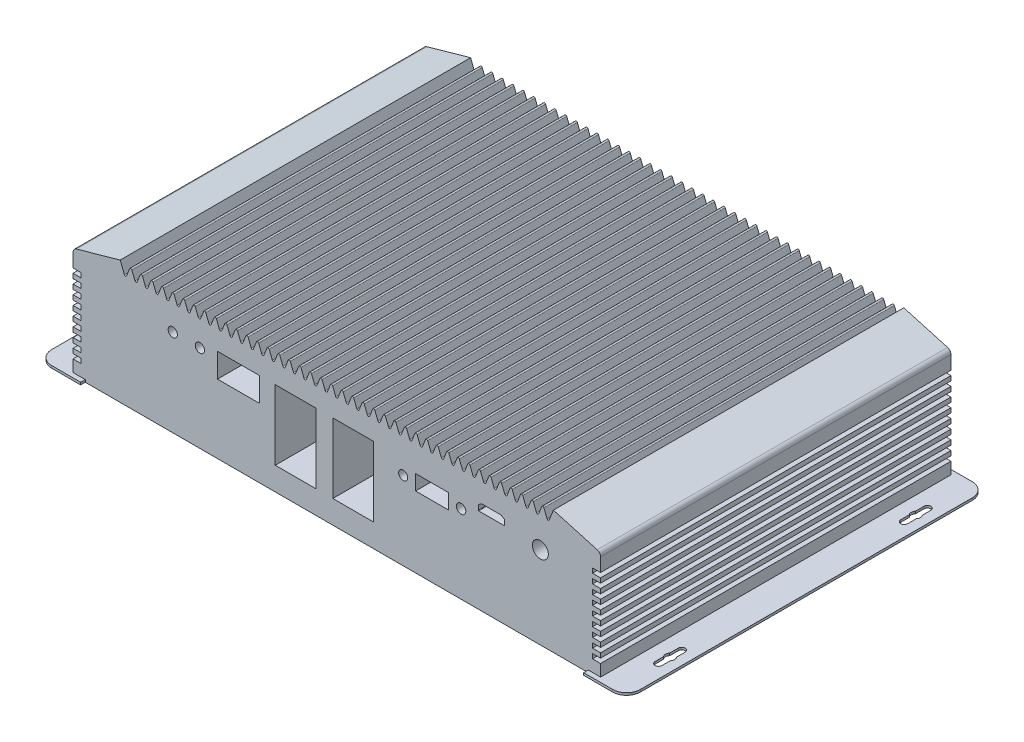
SolidWorks part; units mm, degrees
ref_plane "前视基准面" through (0, 0, 0) normal (0, 0, 1) x (1, 0, 0)
ref_plane "上视基准面" through (0, 0, 0) normal (0, 1, 0) x (1, 0, 0)
ref_plane "右视基准面" through (0, 0, 0) normal (1, 0, 0) x (0, 0, -1)
other "Configuration Table"
sketch "草图1" plane through (0, 0, 0) normal (0, 0, 1) x (1, 0, 0)
  line L0 (0, 0) -> (0, -13.9095) construction
  line L1 (-127.01, 0.5) -> (127.01, 0.5)
  line L2 (-127.01, 0.5) -> (-127.01, -0.5)
  line L3 (-127.01, -0.5) -> (127.01, -0.5)
  line L4 (127.01, 0.5) -> (127.01, -0.5)
  line L5 (-127.01, 0.5) -> (127.01, -0.5) construction
  line L6 (-127.01, -0.5) -> (127.01, 0.5) construction
  line L7 (108.53, 0.5) -> (108.53, 42.3)
  line L8 (108.53, 0.5) -> (-108.53, 0.5)
  line L9 (0, 0.5) -> (0, 46.5)
  line L10 (104.33, 46.5) -> (-104.33, 46.5)
  line L11 (-108.53, 0.5) -> (-108.53, 42.3)
  arc A0 (-104.33, 46.5) -> (-108.53, 42.3) centre (-104.33, 42.3) ccw
  arc A1 (104.33, 46.5) -> (108.53, 42.3) centre (104.33, 42.3) cw
  point P0 (0, 0)
  point P14 (-108.53, 46.5)
  point P19 (108.53, 46.5)
  dimension "D5" = 4.2
  dimension "D1" = 254.02
  dimension "D2" = 1
  dimension "D3" = 108.53
  dimension "D4" = 46
extrude "凸台-拉伸1" add sketch "草图1" against normal blind 155.2 contours L10 A0 L11 L1 L9 | A1 L10 L9 L8 L7 | L4 L1 L8 L2 L3
sketch "草图2" plane through (0, 0, 0) normal (0, 0, 1) x (1, 0, 0)
  line L0 (104.33, 46.5) -> (-104.33, 46.5) construction
  line L1 (104.33, 46.5) -> (-104.33, 46.5)
  line L2 (-108.53, 0.5) -> (-108.53, 42.3) construction
  line L3 (-108.53, 0.5) -> (-108.53, 42.3)
  line L4 (108.53, 0.5) -> (108.53, 42.3) construction
  line L5 (108.53, 0.5) -> (108.53, 42.3)
  line L6 (-127.01, -0.5) -> (127.01, -0.5) construction
  line L8 (-108.53, 0.5) -> (-108.53, -0.5)
  line L9 (-108.53, -0.5) -> (108.53, -0.5)
  line L10 (108.53, 0.5) -> (108.53, -0.5)
  arc A0 (108.53, 42.3) -> (104.33, 46.5) centre (104.33, 42.3) ccw construction
  arc A1 (-104.33, 46.5) -> (-108.53, 42.3) centre (-104.33, 42.3) ccw construction
  arc A2 (108.53, 42.3) -> (104.33, 46.5) centre (104.33, 42.3) ccw
  arc A3 (-104.33, 46.5) -> (-108.53, 42.3) centre (-104.33, 42.3) ccw
extrude "切除-拉伸1" cut sketch "草图2" against normal blind 2
ref_plane "基准面1" through (0, 0, -77.6) normal (0, 0, 1) x (1, 0, 0)
mirror "镜向1" about plane through (0, 0, -77.6) normal (0, 0, 1) of "切除-拉伸1"
sketch "草图3" plane through (0, -0.5, 0) normal (0, -1, 0) x (1, 0, 0)
  line L0 (-127.01, -77.6) -> (126.9569, -77.6) construction
  line L3 (0, -2) -> (0, -161.6283) construction
  line L5 (-121.245, -19.6) -> (-121.245, -29.6) construction
  line L6 (-119.745, -19.6) -> (-119.745, -29.6)
  line L7 (-122.745, -19.6) -> (-122.745, -29.6)
  line L8 (-104.33, -2) -> (104.33, -2)
  line L9 (-104.33, -2) -> (104.33, -2)
  line L10 (104.33, -2) -> (108.53, -2)
  line L11 (104.33, -2) -> (108.53, -2)
  line L12 (108.53, -2) -> (108.53, 0)
  line L13 (108.53, -2) -> (108.53, 0)
  line L14 (108.53, 0) -> (127.01, 0)
  line L15 (108.53, 0) -> (121.01, 0)
  line L16 (127.01, 0) -> (127.01, -155.2)
  line L17 (127.01, -6) -> (127.01, -149.2)
  line L18 (127.01, -155.2) -> (108.53, -155.2)
  line L19 (121.01, -155.2) -> (108.53, -155.2)
  line L20 (108.53, -155.2) -> (108.53, -153.2)
  line L21 (108.53, -155.2) -> (108.53, -153.2)
  line L22 (108.53, -153.2) -> (104.33, -153.2)
  line L23 (108.53, -153.2) -> (104.33, -153.2)
  line L24 (104.33, -153.2) -> (-104.33, -153.2)
  line L25 (104.33, -153.2) -> (-104.33, -153.2)
  line L26 (-104.33, -153.2) -> (-108.53, -153.2)
  line L27 (-104.33, -153.2) -> (-108.53, -153.2)
  line L28 (-108.53, -153.2) -> (-108.53, -155.2)
  line L29 (-108.53, -153.2) -> (-108.53, -155.2)
  line L30 (-108.53, -155.2) -> (-127.01, -155.2)
  line L31 (-108.53, -155.2) -> (-121.01, -155.2)
  line L32 (-127.01, -155.2) -> (-127.01, 0)
  line L33 (-127.01, -149.2) -> (-127.01, -6)
  line L34 (-127.01, 0) -> (-108.53, 0)
  line L35 (-121.01, 0) -> (-108.53, 0)
  line L36 (-108.53, 0) -> (-108.53, -2)
  line L37 (-108.53, 0) -> (-108.53, -2)
  line L38 (-108.53, -2) -> (-104.33, -2)
  line L39 (-108.53, -2) -> (-104.33, -2)
  line L40 (-121.245, -135.6) -> (-121.245, -125.6) construction
  line L41 (-127.01, 0) -> (-121.01, 0)
  line L42 (-127.01, 0) -> (-127.01, -6)
  line L43 (-127.01, -6) -> (-121.01, -6)
  line L44 (-121.01, 0) -> (-121.01, -6)
  line L45 (-127.01, -155.2) -> (-121.01, -155.2)
  line L46 (-127.01, -155.2) -> (-127.01, -149.2)
  line L47 (-127.01, -149.2) -> (-121.01, -149.2)
  line L48 (-121.01, -155.2) -> (-121.01, -149.2)
  line L49 (127.01, -155.2) -> (121.01, -155.2)
  line L50 (127.01, -155.2) -> (127.01, -149.2)
  line L51 (127.01, -149.2) -> (121.01, -149.2)
  line L52 (121.01, -155.2) -> (121.01, -149.2)
  line L53 (127.01, 0) -> (121.01, 0)
  line L54 (127.01, 0) -> (127.01, -6)
  line L55 (127.01, -6) -> (121.01, -6)
  line L56 (121.01, 0) -> (121.01, -6)
  line L57 (-119.745, -135.6) -> (-119.745, -125.6)
  line L58 (-122.745, -135.6) -> (-122.745, -125.6)
  line L59 (121.245, -135.6) -> (121.245, -125.6) construction
  line L60 (119.745, -135.6) -> (119.745, -125.6)
  line L61 (122.745, -135.6) -> (122.745, -125.6)
  line L62 (121.245, -19.6) -> (121.245, -29.6) construction
  line L63 (119.745, -19.6) -> (119.745, -29.6)
  line L64 (122.745, -19.6) -> (122.745, -29.6)
  circle A0 centre (-121.245, -24.6) radius 2
  arc A1 (-119.745, -19.6) -> (-122.745, -19.6) centre (-121.245, -19.6) ccw
  arc A2 (-122.745, -29.6) -> (-119.745, -29.6) centre (-121.245, -29.6) ccw
  arc A3 (-127.01, -6) -> (-121.01, 0) centre (-121.01, -6) cw
  arc A4 (121.01, 0) -> (127.01, -6) centre (121.01, -6) cw
  arc A5 (127.01, -149.2) -> (121.01, -155.2) centre (121.01, -149.2) cw
  arc A6 (-121.01, -155.2) -> (-127.01, -149.2) centre (-121.01, -149.2) cw
  circle A7 centre (-121.245, -130.6) radius 2
  arc A8 (-119.745, -135.6) -> (-122.745, -135.6) centre (-121.245, -135.6) cw
  arc A9 (-122.745, -125.6) -> (-119.745, -125.6) centre (-121.245, -125.6) cw
  circle A10 centre (121.245, -130.6) radius 2
  circle A11 centre (121.245, -24.6) radius 2
  arc A12 (119.745, -135.6) -> (122.745, -135.6) centre (121.245, -135.6) ccw
  arc A13 (122.745, -125.6) -> (119.745, -125.6) centre (121.245, -125.6) ccw
  arc A14 (119.745, -19.6) -> (122.745, -19.6) centre (121.245, -19.6) cw
  arc A15 (122.745, -29.6) -> (119.745, -29.6) centre (121.245, -29.6) cw
  point P9 (-121.245, -24.6)
  point P54 (-121.245, -130.6)
  point P65 (121.245, -130.6)
  point P72 (121.245, -24.6)
  line M4 (-127.01, -155.2) -> (-108.53, -155.2)
  line M8 (108.53, -155.2) -> (127.01, -155.2)
  line M9 (127.01, -155.2) -> (127.01, 0)
  line M10 (127.01, 0) -> (108.53, 0)
  line M14 (-108.53, 0) -> (-127.01, 0)
  line M15 (-127.01, 0) -> (-127.01, -155.2)
  dimension "D1" = 4
  dimension "D2" = 53
  dimension "D3" = 121.245
  dimension "D4" = 6
  dimension "D5" = 6
extrude "切除-拉伸2" cut sketch "草图3" against normal blind 2 contours A3 M15 M14 | A6 M4 M15 | A4 M10 M9 | L6 A1 L7 A0 | L6 A0 L7 | L7 A0 | L6 A0 | L7 A2 L6 A0 | A9 L58 A7 L57 | A7 L58 L57 | A7 L58 | A8 L57 A7 L58 | A14 L63 A11 L64 | A15 L64 A11 L63 | A5 M9 M8 | L61 A13 L60 A12 | A10
sketch "草图5" plane through (0, 0, -2) normal (0, 0, 1) x (1, 0, 0)
  line L0 (-108.53, -0.5) -> (108.53, -0.5) construction
  line L1 (0, -0.5) -> (-113.815, -0.5)
  line L2 (0, -0.5) -> (0, 52.72)
  line L4 (-113.815, -0.5) -> (-113.815, 5.5781)
  line L5 (-113.815, 11.5781) -> (-110.315, 11.5781)
  line L6 (-113.815, 7.5781) -> (-110.315, 7.5781)
  line L8 (-113.815, 5.5781) -> (-110.315, 5.5781)
  line L9 (-110.315, 7.5781) -> (-110.315, 5.5781)
  line L10 (-110.315, 11.5781) -> (-110.315, 9.5781)
  line L11 (-113.815, 9.5781) -> (-110.315, 9.5781)
  line L12 (-113.815, 15.5781) -> (-110.315, 15.5781)
  line L13 (-110.315, 15.5781) -> (-110.315, 13.5781)
  line L14 (-113.815, 13.5781) -> (-110.315, 13.5781)
  line L15 (-113.815, 19.5781) -> (-110.315, 19.5781)
  line L16 (-110.315, 19.5781) -> (-110.315, 17.5781)
  line L17 (-113.815, 17.5781) -> (-110.315, 17.5781)
  line L18 (-113.815, 23.5781) -> (-110.315, 23.5781)
  line L19 (-110.315, 23.5781) -> (-110.315, 21.5781)
  line L20 (-113.815, 21.5781) -> (-110.315, 21.5781)
  line L21 (-113.815, 27.5781) -> (-110.315, 27.5781)
  line L22 (-110.315, 27.5781) -> (-110.315, 25.5781)
  line L23 (-113.815, 25.5781) -> (-110.315, 25.5781)
  line L24 (-113.815, 31.5781) -> (-110.315, 31.5781)
  line L25 (-110.315, 31.5781) -> (-110.315, 29.5781)
  line L26 (-113.815, 29.5781) -> (-110.315, 29.5781)
  line L27 (-113.815, 35.5781) -> (-110.315, 35.5781)
  line L28 (-110.315, 35.5781) -> (-110.315, 33.5781)
  line L29 (-113.815, 33.5781) -> (-110.315, 33.5781)
  line L30 (-113.815, 39.5781) -> (-110.315, 39.5781)
  line L31 (-110.315, 39.5781) -> (-110.315, 37.5781)
  line L32 (-113.815, 37.5781) -> (-110.315, 37.5781)
  line L33 (-113.815, 39.5781) -> (-113.815, 45.4567)
  line L34 (-113.815, 35.5781) -> (-113.815, 37.5781)
  line L35 (-113.815, 31.5781) -> (-113.815, 33.5781)
  line L36 (-113.815, 27.5781) -> (-113.815, 29.5781)
  line L37 (-113.815, 23.5781) -> (-113.815, 25.5781)
  line L38 (-113.815, 19.5781) -> (-113.815, 21.5781)
  line L39 (-113.815, 15.5781) -> (-113.815, 17.5781)
  line L40 (-113.815, 11.5781) -> (-113.815, 13.5781)
  line L41 (-113.815, 7.5781) -> (-113.815, 9.5781)
  line L42 (0, 46.97) -> (-1.7969, 51.5463)
  line L43 (-2.7265, 51.5494) -> (-4.0913, 48.1406)
  line L44 (-5.0209, 48.1437) -> (-6.3569, 51.5463)
  line L45 (-7.2865, 51.5494) -> (-8.6513, 48.1406)
  line L46 (-9.5809, 48.1437) -> (-10.9169, 51.5463)
  line L47 (-4.56, 46.97) -> (-6.3569, 51.5463)
  line L48 (-11.8465, 51.5494) -> (-13.2113, 48.1406)
  line L49 (-14.1409, 48.1437) -> (-15.4769, 51.5463)
  line L50 (-9.5809, 48.1437) -> (-10.9169, 51.5463)
  line L51 (-16.4065, 51.5494) -> (-17.7713, 48.1406)
  line L52 (-18.7009, 48.1437) -> (-20.0369, 51.5463)
  line L53 (-14.1409, 48.1437) -> (-15.4769, 51.5463)
  line L54 (-20.9665, 51.5494) -> (-22.3313, 48.1406)
  line L55 (-23.2609, 48.1437) -> (-24.5969, 51.5463)
  line L56 (-18.7009, 48.1437) -> (-20.0369, 51.5463)
  line L57 (-25.5265, 51.5494) -> (-26.8913, 48.1406)
  line L58 (-27.8209, 48.1437) -> (-29.1569, 51.5463)
  line L59 (-23.2609, 48.1437) -> (-24.5969, 51.5463)
  line L60 (-30.0865, 51.5494) -> (-31.4513, 48.1406)
  line L61 (-32.3809, 48.1437) -> (-33.7169, 51.5463)
  line L62 (-27.8209, 48.1437) -> (-29.1569, 51.5463)
  line L63 (-34.6465, 51.5494) -> (-36.0113, 48.1406)
  line L64 (-36.9409, 48.1437) -> (-38.2769, 51.5463)
  line L65 (-32.3809, 48.1437) -> (-33.7169, 51.5463)
  line L66 (-39.2065, 51.5494) -> (-40.5713, 48.1406)
  line L67 (-41.5009, 48.1437) -> (-42.8369, 51.5463)
  line L68 (-36.9409, 48.1437) -> (-38.2769, 51.5463)
  line L69 (-43.7665, 51.5494) -> (-45.1313, 48.1406)
  line L70 (-46.0609, 48.1437) -> (-47.3969, 51.5463)
  line L71 (-41.5009, 48.1437) -> (-42.8369, 51.5463)
  line L72 (-48.3265, 51.5494) -> (-49.6913, 48.1406)
  line L73 (-50.6209, 48.1437) -> (-51.9569, 51.5463)
  line L74 (-46.0609, 48.1437) -> (-47.3969, 51.5463)
  line L75 (-52.8865, 51.5494) -> (-54.2513, 48.1406)
  line L76 (-55.1809, 48.1437) -> (-56.5169, 51.5463)
  line L77 (-50.6209, 48.1437) -> (-51.9569, 51.5463)
  line L78 (-57.4465, 51.5494) -> (-58.8113, 48.1406)
  line L79 (-59.7409, 48.1437) -> (-61.0769, 51.5463)
  line L80 (-55.1809, 48.1437) -> (-56.5169, 51.5463)
  line L81 (-62.0065, 51.5494) -> (-63.3713, 48.1406)
  line L82 (-64.3009, 48.1437) -> (-65.6369, 51.5463)
  line L83 (-59.7409, 48.1437) -> (-61.0769, 51.5463)
  line L84 (-66.5665, 51.5494) -> (-67.9313, 48.1406)
  line L85 (-68.8609, 48.1437) -> (-70.1969, 51.5463)
  line L86 (-64.3009, 48.1437) -> (-65.6369, 51.5463)
  line L87 (-71.1265, 51.5494) -> (-72.4913, 48.1406)
  line L88 (-73.4209, 48.1437) -> (-74.7569, 51.5463)
  line L89 (-68.8609, 48.1437) -> (-70.1969, 51.5463)
  line L90 (-75.6865, 51.5494) -> (-77.0513, 48.1406)
  line L91 (-77.9809, 48.1437) -> (-79.3169, 51.5463)
  line L92 (-73.4209, 48.1437) -> (-74.7569, 51.5463)
  line L93 (-80.2465, 51.5494) -> (-81.6113, 48.1406)
  line L94 (-82.5409, 48.1437) -> (-83.8769, 51.5463)
  line L95 (-77.9809, 48.1437) -> (-79.3169, 51.5463)
  line L96 (-84.8065, 51.5494) -> (-86.1713, 48.1406)
  line L97 (-87.1009, 48.1437) -> (-88.4369, 51.5463)
  line L98 (-82.5409, 48.1437) -> (-83.8769, 51.5463)
  line L99 (-89.3665, 51.5494) -> (-90.7313, 48.1406)
  line L100 (-91.6609, 48.1437) -> (-93.4578, 52.72)
  line L101 (-87.1009, 48.1437) -> (-88.4369, 51.5463)
  line L102 (-93.4578, 52.72) -> (-112.3586, 47.3814)
  arc A0 (-1.7969, 51.5463) -> (-2.7265, 51.5494) centre (-2.2623, 51.3635) ccw
  arc A1 (-4.0913, 48.1406) -> (-5.0209, 48.1437) centre (-4.5555, 48.3265) cw
  arc A2 (-6.3569, 51.5463) -> (-7.2865, 51.5494) centre (-6.8223, 51.3635) ccw
  arc A3 (-8.6513, 48.1406) -> (-9.5809, 48.1437) centre (-9.1155, 48.3265) cw
  arc A4 (-10.9169, 51.5463) -> (-11.8465, 51.5494) centre (-11.3823, 51.3635) ccw
  arc A5 (-13.2113, 48.1406) -> (-14.1409, 48.1437) centre (-13.6755, 48.3265) cw
  arc A6 (-15.4769, 51.5463) -> (-16.4065, 51.5494) centre (-15.9423, 51.3635) ccw
  arc A7 (-17.7713, 48.1406) -> (-18.7009, 48.1437) centre (-18.2355, 48.3265) cw
  arc A8 (-20.0369, 51.5463) -> (-20.9665, 51.5494) centre (-20.5023, 51.3635) ccw
  arc A9 (-22.3313, 48.1406) -> (-23.2609, 48.1437) centre (-22.7955, 48.3265) cw
  arc A10 (-24.5969, 51.5463) -> (-25.5265, 51.5494) centre (-25.0623, 51.3635) ccw
  arc A11 (-26.8913, 48.1406) -> (-27.8209, 48.1437) centre (-27.3555, 48.3265) cw
  arc A12 (-29.1569, 51.5463) -> (-30.0865, 51.5494) centre (-29.6223, 51.3635) ccw
  arc A13 (-31.4513, 48.1406) -> (-32.3809, 48.1437) centre (-31.9155, 48.3265) cw
  arc A14 (-33.7169, 51.5463) -> (-34.6465, 51.5494) centre (-34.1823, 51.3635) ccw
  arc A15 (-36.0113, 48.1406) -> (-36.9409, 48.1437) centre (-36.4755, 48.3265) cw
  arc A16 (-38.2769, 51.5463) -> (-39.2065, 51.5494) centre (-38.7423, 51.3635) ccw
  arc A17 (-40.5713, 48.1406) -> (-41.5009, 48.1437) centre (-41.0355, 48.3265) cw
  arc A18 (-42.8369, 51.5463) -> (-43.7665, 51.5494) centre (-43.3023, 51.3635) ccw
  arc A19 (-45.1313, 48.1406) -> (-46.0609, 48.1437) centre (-45.5955, 48.3265) cw
  arc A20 (-47.3969, 51.5463) -> (-48.3265, 51.5494) centre (-47.8623, 51.3635) ccw
  arc A21 (-49.6913, 48.1406) -> (-50.6209, 48.1437) centre (-50.1555, 48.3265) cw
  arc A22 (-51.9569, 51.5463) -> (-52.8865, 51.5494) centre (-52.4223, 51.3635) ccw
  arc A23 (-54.2513, 48.1406) -> (-55.1809, 48.1437) centre (-54.7155, 48.3265) cw
  arc A24 (-56.5169, 51.5463) -> (-57.4465, 51.5494) centre (-56.9823, 51.3635) ccw
  arc A25 (-58.8113, 48.1406) -> (-59.7409, 48.1437) centre (-59.2755, 48.3265) cw
  arc A26 (-61.0769, 51.5463) -> (-62.0065, 51.5494) centre (-61.5423, 51.3635) ccw
  arc A27 (-63.3713, 48.1406) -> (-64.3009, 48.1437) centre (-63.8355, 48.3265) cw
  arc A28 (-65.6369, 51.5463) -> (-66.5665, 51.5494) centre (-66.1023, 51.3635) ccw
  arc A29 (-67.9313, 48.1406) -> (-68.8609, 48.1437) centre (-68.3955, 48.3265) cw
  arc A30 (-70.1969, 51.5463) -> (-71.1265, 51.5494) centre (-70.6623, 51.3635) ccw
  arc A31 (-72.4913, 48.1406) -> (-73.4209, 48.1437) centre (-72.9555, 48.3265) cw
  arc A32 (-74.7569, 51.5463) -> (-75.6865, 51.5494) centre (-75.2223, 51.3635) ccw
  arc A33 (-77.0513, 48.1406) -> (-77.9809, 48.1437) centre (-77.5155, 48.3265) cw
  arc A34 (-79.3169, 51.5463) -> (-80.2465, 51.5494) centre (-79.7823, 51.3635) ccw
  arc A35 (-81.6113, 48.1406) -> (-82.5409, 48.1437) centre (-82.0755, 48.3265) cw
  arc A36 (-83.8769, 51.5463) -> (-84.8065, 51.5494) centre (-84.3423, 51.3635) ccw
  arc A37 (-86.1713, 48.1406) -> (-87.1009, 48.1437) centre (-86.6355, 48.3265) cw
  arc A38 (-88.4369, 51.5463) -> (-89.3665, 51.5494) centre (-88.9023, 51.3635) ccw
  arc A39 (-90.7313, 48.1406) -> (-91.6609, 48.1437) centre (-91.1955, 48.3265) cw
  arc A40 (-112.3586, 47.3814) -> (-113.815, 45.4567) centre (-111.815, 45.4567) ccw
  point P47 (-2.2578, 52.72)
  point P51 (-4.56, 46.97)
  dimension "D9" = 0.5
  dimension "D11" = 0.5
  dimension "D2" = 2
  dimension "D3" = 2
  dimension "D4" = 3.5
  dimension "D6" = 4.56
  dimension "D7" = 5.75
  dimension "D8" = 5.75
  dimension "D5" = 9
  dimension "D12" = 20
extrude "凸台-拉伸2" add sketch "草图5" against normal up to surface (151.2 mm away) up to face at (0, 22.4175, -153.2)
mirror "镜向2" about plane through (0, 0, 0) normal (1, 0, 0) of "凸台-拉伸2"
fillet "圆角1" radius 0.5 1 edges at (0, 46.97, -77.6)
sketch "草图6" plane through (0, 0, -2) normal (0, 0, 1) x (1, 0, 0)
  line L1 (-51.4784, 39.6056) -> (-33.2484, 39.6056)
  line L2 (-51.4784, 39.6056) -> (-51.4784, 29.2056)
  line L3 (-51.4784, 29.2056) -> (-33.2484, 29.2056)
  line L4 (-33.2484, 39.6056) -> (-33.2484, 29.2056)
  line L9 (72.3539, 38.665) -> (70.9933, 39.572)
  line L10 (72.3539, 38.665) -> (70.9933, 39.572) construction
  line L11 (70.8824, 39.6056) -> (62.6035, 39.6056)
  line L12 (62.6035, 39.6056) -> (70.8824, 39.6056) construction
  line L13 (66.7429, 39.6056) -> (66.7429, 37.5021) construction
  line L14 (61.132, 38.665) -> (62.4925, 39.572)
  line L20 (61.0429, 36.5056) -> (61.0429, 38.4985)
  line L22 (72.2429, 36.3056) -> (61.2429, 36.3056)
  line L23 (72.4429, 38.4985) -> (72.4429, 36.5056)
  line L25 (33.989, 36.6541) -> (48.2018, 36.6541)
  line L26 (33.989, 36.6541) -> (33.989, 30.1337)
  line L27 (33.989, 30.1337) -> (48.2018, 30.1337)
  line L28 (48.2018, 36.6541) -> (48.2018, 30.1337)
  line L29 (-26.5627, 39.6056) -> (-9.0569, 39.6056)
  line L30 (-26.5627, 39.6056) -> (-26.5627, 9.4748)
  line L31 (-26.5627, 9.4748) -> (-9.0569, 9.4748)
  line L32 (-9.0569, 39.6056) -> (-9.0569, 9.4748)
  line L33 (-1.7185, 9.4748) -> (15.7873, 9.4748)
  line L34 (-1.7185, 9.4748) -> (-1.7185, 39.6056)
  line L35 (-1.7185, 39.6056) -> (15.7873, 39.6056)
  line L36 (15.7873, 9.4748) -> (15.7873, 39.6056)
  circle A4 centre (-70.7805, 37.1056) radius 2
  circle A5 centre (-59.0805, 37.1056) radius 2
  circle A6 centre (87.8353, 35.1056) radius 3.45
  arc A8 (70.9933, 39.572) -> (70.8824, 39.6056) centre (70.8824, 39.4056) ccw
  arc A9 (62.4925, 39.572) -> (62.6035, 39.6056) centre (62.6035, 39.4056) cw
  arc A10 (61.0429, 36.5056) -> (61.2429, 36.3056) centre (61.2429, 36.5056) ccw
  arc A11 (72.2429, 36.3056) -> (72.4429, 36.5056) centre (72.2429, 36.5056) ccw
  arc A12 (72.4429, 38.4985) -> (72.3539, 38.665) centre (72.2429, 38.4985) ccw
  arc A13 (61.132, 38.665) -> (61.0429, 38.4985) centre (61.2429, 38.4985) ccw
  arc A14 (47.2978, 29.5611) -> (48.2813, 30.3806) centre (47.2978, 30.5611) ccw construction
  circle A15 centre (28.6309, 33.3306) radius 1.9448
  circle A16 centre (53.6309, 33.3306) radius 2.0338
  point P19 (70.9429, 39.6056)
  point P24 (62.5429, 39.6056)
  point P37 (61.0429, 36.3056)
  point P42 (72.4429, 36.3056)
  point P45 (72.4429, 38.6056)
  point P48 (61.0429, 38.6056)
  dimension "D1" = 0.2
extrude "切除-拉伸3" cut sketch "草图6" against normal blind 20
sketch "草图7" plane through (0, 0, -153.2) normal (0, 0, -1) x (-1, 0, 0)
  line L0 (-46.5904, 18.3426) -> (-8.4681, 18.3426)
  line L1 (-89.3801, 41.4235) -> (-74.7501, 41.4235)
  line L2 (-89.3801, 41.4235) -> (-89.3801, 11.8335)
  line L3 (-89.3801, 11.8335) -> (-74.7501, 11.8335)
  line L4 (-74.7501, 41.4235) -> (-74.7501, 11.8335)
  line L5 (-67.9881, 41.4235) -> (-54.127, 41.4235)
  line L6 (-67.9881, 41.4235) -> (-67.9881, 26.3854)
  line L7 (-67.9881, 26.3854) -> (-54.127, 26.3854)
  line L8 (-54.127, 41.4235) -> (-54.127, 26.3854)
  line L9 (-46.5916, 41.4235) -> (-8.4693, 41.4235)
  line L10 (-46.5916, 41.4235) -> (-46.5916, 29.3289)
  line L11 (-46.5916, 29.3289) -> (-8.4693, 29.3289)
  line L12 (-8.4693, 41.4235) -> (-8.4693, 29.3289)
  line L13 (-46.5904, 18.3426) -> (-46.5904, 6.248)
  line L14 (-46.5904, 6.248) -> (-8.4681, 6.248)
  line L15 (-8.4681, 18.3426) -> (-8.4681, 6.248)
  line L16 (-1.5668, 18.4092) -> (36.5555, 18.4092)
  line L17 (-1.568, 41.4901) -> (36.5543, 41.4901)
  line L18 (-1.568, 41.4901) -> (-1.568, 29.3955)
  line L19 (-1.568, 29.3955) -> (36.5543, 29.3955)
  line L20 (36.5543, 41.4901) -> (36.5543, 29.3955)
  line L21 (-1.5668, 18.4092) -> (-1.5668, 6.3146)
  line L22 (-1.5668, 6.3146) -> (36.5555, 6.3146)
  line L23 (36.5555, 18.4092) -> (36.5555, 6.3146)
  line L24 (43.3143, 18.3588) -> (81.4366, 18.3588)
  line L25 (43.3132, 41.4397) -> (81.4355, 41.4397)
  line L26 (43.3132, 41.4397) -> (43.3132, 29.3451)
  line L27 (43.3132, 29.3451) -> (81.4355, 29.3451)
  line L28 (81.4355, 41.4397) -> (81.4355, 29.3451)
  line L29 (43.3143, 18.3588) -> (43.3143, 6.2642)
  line L30 (43.3143, 6.2642) -> (81.4366, 6.2642)
  line L31 (81.4366, 18.3588) -> (81.4366, 6.2642)
extrude "切除-拉伸4" cut sketch "草图7" against normal blind 20
